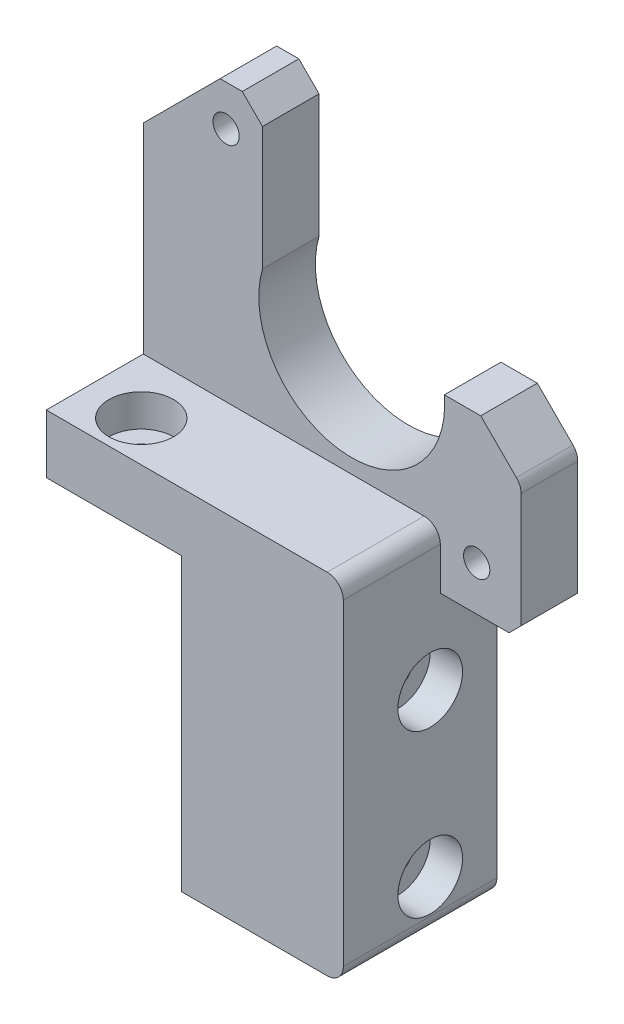
SolidWorks part; units mm, degrees
ref_plane "Front Plane" through (0, 0, 0) normal (0, 0, 1) x (1, 0, 0)
ref_plane "Top Plane" through (0, 0, 0) normal (0, 1, 0) x (1, 0, 0)
ref_plane "Right Plane" through (0, 0, 0) normal (1, 0, 0) x (0, 0, -1)
sketch "Sketch1" plane through (0, 0, 0) normal (0, 0, 1) x (1, 0, 0)
  line L0 (0, 0) -> (20, 0)
  line L1 (20, 0) -> (20, 43.25)
  line L2 (20, 43.25) -> (-16.75, 43.25)
  line L3 (-16.75, 43.25) -> (-16.75, 36)
  line L4 (-16.75, 36) -> (0, 36)
  line L5 (0, 36) -> (0, 0)
  dimension "D1" = 20
  dimension "D2" = 43.25
  dimension "D3" = 16.75
  dimension "D4" = 36
extrude "Boss-Extrude1" add sketch "Sketch1" along normal blind 19
sketch "Sketch2" plane through (0, 0, 0) normal (0, 0, -1) x (-1, 0, 0)
  line L0 (-20, 36) -> (16.75, 36)
  line L1 (16.75, 36) -> (16.75, 68)
  line L2 (16.75, 68) -> (7.25, 77.5)
  line L3 (7.25, 77.5) -> (4.5, 77.5)
  line L4 (4.5, 77.5) -> (2, 75)
  line L5 (2, 75) -> (2, 59.75)
  line L7 (-20, 0) -> (-20, 43.25) construction
  line L8 (-20, 36) -> (-28.5, 36)
  line L9 (-28.5, 36) -> (-30, 37.5)
  line L10 (-30, 37.5) -> (-30, 52.5)
  line L11 (-30, 52.5) -> (-25, 57.5)
  line L12 (-25, 57.5) -> (-20.5, 57.5)
  arc A0 (-20.5, 57.5) -> (2, 59.75) centre (-9.0408, 56.5326) ccw
  dimension "D16" = 23
  dimension "D1" = 45
  dimension "D2" = 32
  dimension "D3" = 9.5
  dimension "D4" = 2.75
  dimension "D5" = 45
  dimension "D6" = 2.5
  dimension "D7" = 15.25
  dimension "D9" = 8.5
  dimension "D10" = 135
  dimension "D11" = 1.5
  dimension "D12" = 15
  dimension "D13" = 45
  dimension "D14" = 5
  dimension "D15" = 4.5
extrude "Boss-Extrude2" add sketch "Sketch2" against normal blind 7
sketch "Sketch3" plane through (20, 0, 0) normal (1, 0, 0) x (0, 0, -1)
  line L0 (0, 0) -> (0, 36) construction
  line L1 (-8.25, 26.25) -> (-8.25, 6.25) construction
  line L2 (-19, 0) -> (0, 0) construction
  circle A0 centre (-8.25, 26.25) radius 1.75
  circle A1 centre (-8.25, 6.25) radius 1.75
  dimension "D4" = 3.5
  dimension "D1" = 8.25
  dimension "D2" = 26.25
  dimension "D3" = 6.25
extrude "Cut-Extrude1" cut sketch "Sketch3" against normal through all
sketch "Sketch6" plane through (20, 0, 0) normal (1, 0, 0) x (0, 0, -1)
  circle A0 centre (-8.25, 26.25) radius 4
  circle A1 centre (-8.25, 6.25) radius 4
  dimension "D1" = 8
extrude "Cut-Extrude4" cut sketch "Sketch6" against normal blind 4
sketch "Sketch7" plane through (0, 0, 0) normal (0, 0, -1) x (-1, 0, 0)
  line L0 (-28.5, 36) -> (-20, 36) construction
  line L1 (-30, 52.5) -> (-30, 37.5) construction
  line L2 (16.75, 36) -> (0, 36) construction
  circle A0 centre (6.5, 72.5) radius 1.625
  circle A1 centre (-24.5, 41.5) radius 1.625
  dimension "D1" = 3.25
  dimension "D2" = 3.25
  dimension "D3" = 5.5
  dimension "D4" = 5.5
  dimension "D5" = 36.5
  dimension "D6" = 36.5
extrude "Cut-Extrude5" cut sketch "Sketch7" against normal through all
fillet "Fillet1" radius 2 3 edges at (20, 43.25, 13) (30, 52.5, 3.5) (20, 0, 9.5)
sketch "Sketch8" plane through (0, 36, 0) normal (0, -1, 0) x (1, 0, 0)
  line L0 (0, 19) -> (0, 0) construction
  line L1 (-16.75, 0) -> (0, 0) construction
  circle A0 centre (-10, 14) radius 1.75
  dimension "D1" = 10
  dimension "D2" = 14
extrude "Cut-Extrude6" cut sketch "Sketch8" against normal blind 10
sketch "Sketch9" plane through (0, 43.25, 0) normal (0, 1, 0) x (1, 0, 0)
  circle A0 centre (-10, -14) radius 4
extrude "Cut-Extrude7" cut sketch "Sketch9" against normal blind 4
